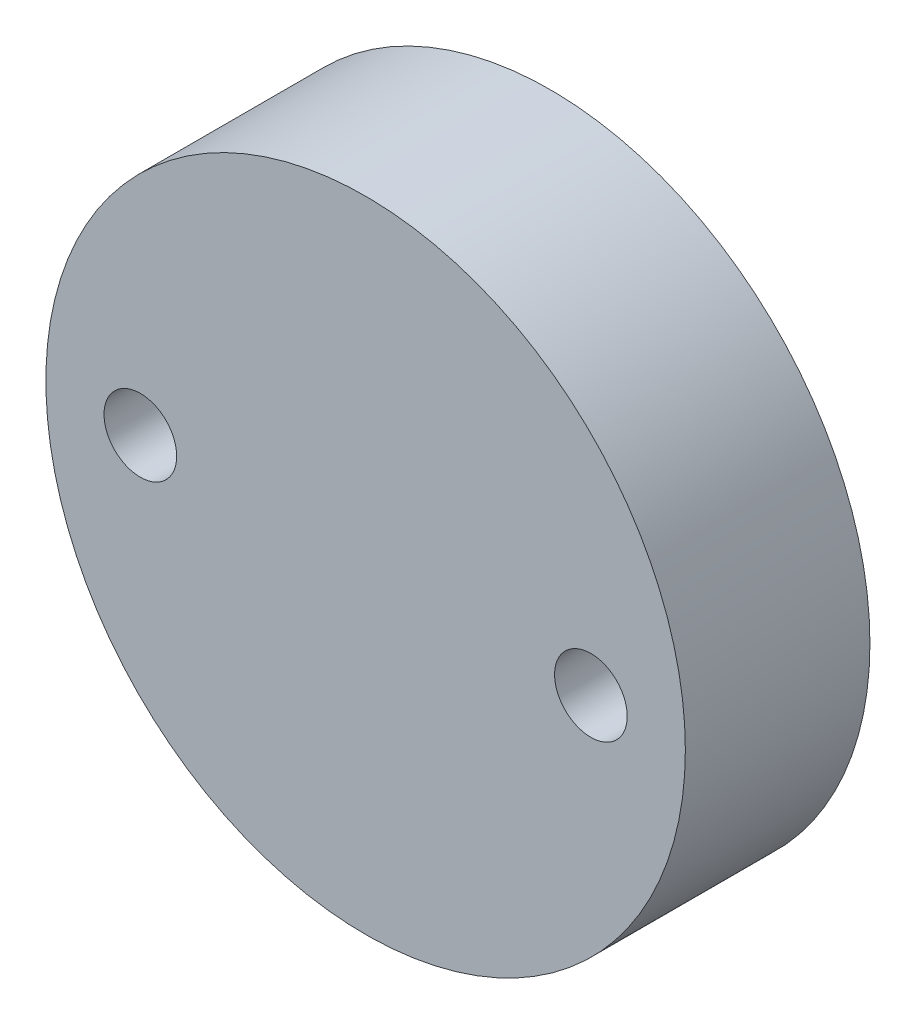
SolidWorks part; units mm, degrees
ref_plane "Front" through (0, 0, 0) normal (0, 0, 1) x (1, 0, 0)
ref_plane "Top" through (0, 0, 0) normal (0, 1, 0) x (1, 0, 0)
ref_plane "Right" through (0, 0, 0) normal (1, 0, 0) x (0, 0, -1)
sketch "Sketch1" plane through (0, 0, 0) normal (0, 0, 1) x (1, 0, 0)
  line L0 (0, 0) -> (-11, 0) construction
  line L1 (0, 0) -> (11, 0) construction
  line L2 (0, 11) -> (0, -11) construction
  circle A0 centre (0, 0) radius 11
  circle A1 centre (-7.75, 0) radius 1.25
  circle A2 centre (7.75, 0) radius 1.25
  dimension "D1" = 22
  dimension "D2" = 2.5
  dimension "D3" = 7.75
extrude "Boss-Extrude1" add sketch "Sketch1" along normal blind 6.35
